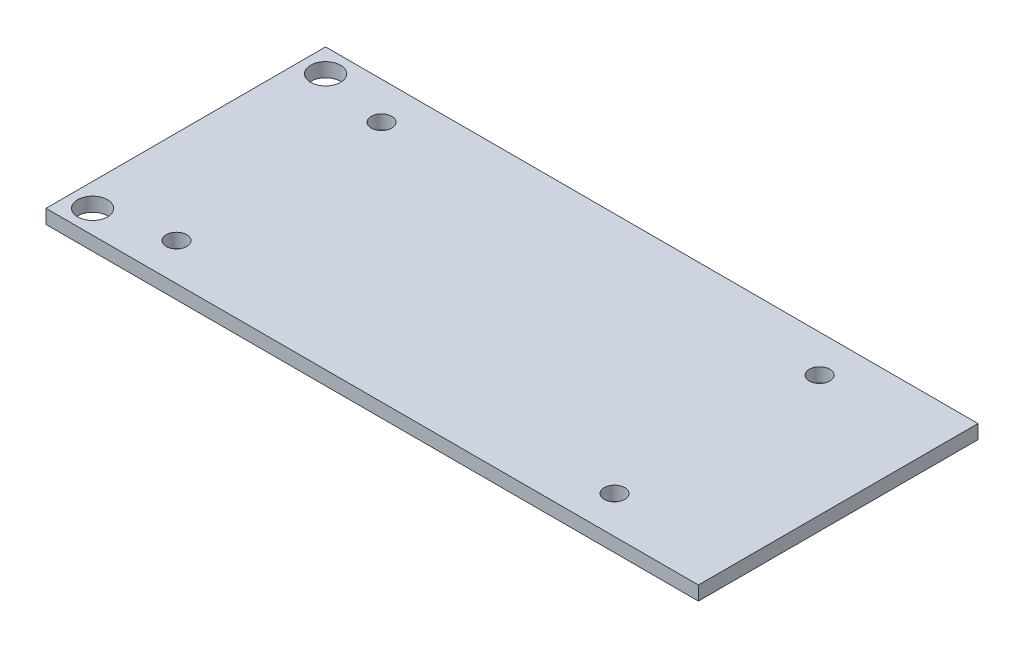
SolidWorks part; units mm, degrees
ref_plane "Спереди" through (0, 0, 0) normal (0, 0, 1) x (1, 0, 0)
ref_plane "Сверху" through (0, 0, 0) normal (0, 1, 0) x (1, 0, 0)
ref_plane "Справа" through (0, 0, 0) normal (1, 0, 0) x (0, 0, -1)
sketch "Эскиз1" plane through (0, 0, 0) normal (0, 1, 0) x (1, 0, 0)
  line L0 (-1.3896, 15) -> (62.2633, 15) construction
  line L1 (0, 0) -> (70, 0)
  line L2 (0, 0) -> (0, 30)
  line L3 (0, 30) -> (70, 30)
  line L4 (70, 0) -> (70, 30)
  circle A0 centre (10, 4) radius 1.1
  circle A1 centre (57, 4) radius 1.1
  circle A2 centre (57, 26) radius 1.1
  circle A3 centre (10, 26) radius 1.1
  circle A4 centre (2.5, 2.5) radius 1.6
  circle A5 centre (2.5, 27.5) radius 1.6
  dimension "D1" = 70
  dimension "D2" = 30
  dimension "D3" = 4
  dimension "D4" = 10
  dimension "D5" = 2
  dimension "D6" = 2
extrude "Бобышка-Вытянуть1" add sketch "Эскиз1" along normal blind 1.5
